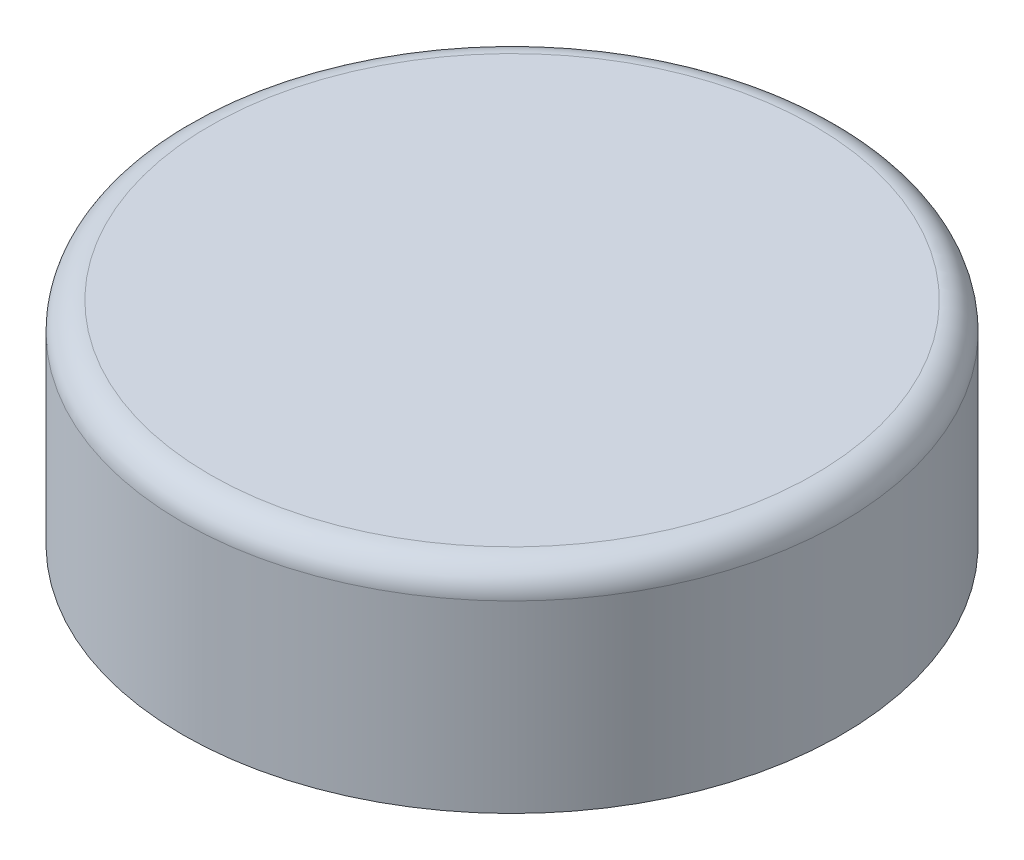
SolidWorks part; units mm, degrees
ref_plane "Front Plane" through (0, 0, 0) normal (0, 0, 1) x (1, 0, 0)
ref_plane "Top Plane" through (0, 0, 0) normal (0, 1, 0) x (1, 0, 0)
ref_plane "Right Plane" through (0, 0, 0) normal (1, 0, 0) x (0, 0, -1)
sketch "Sketch1" plane through (0, 0, 0) normal (0, 1, 0) x (1, 0, 0)
  circle A0 centre (0, 0) radius 30.48
  dimension "D1" = 60.96
extrude "Boss-Extrude1" add sketch "Sketch1" along normal blind 19.558
fillet "Fillet1" radius 2.54 1 edges at (0, 19.558, 30.48)
